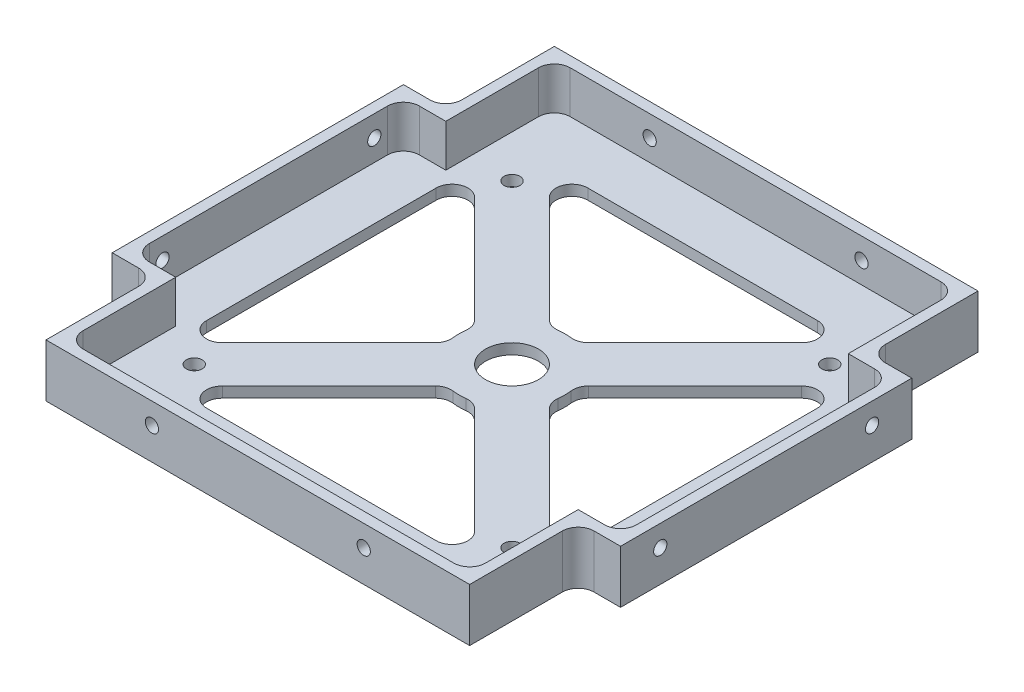
SolidWorks part; units mm, degrees
material "6061-T6 (SS)"
ref_plane "Front Plane" through (0, 0, 0) normal (0, 0, 1) x (1, 0, 0)
ref_plane "Top Plane" through (0, 0, 0) normal (0, 1, 0) x (1, 0, 0)
ref_plane "Right Plane" through (0, 0, 0) normal (1, 0, 0) x (0, 0, -1)
sketch "Sketch1" plane through (0, 0, 0) normal (0, 1, 0) x (1, 0, 0)
  line L0 (0, 8) -> (8, 0)
  line L1 (0, 0) -> (96, 0)
  line L2 (0, 0) -> (0, 96)
  line L3 (0, 96) -> (96, 96)
  line L4 (96, 0) -> (96, 96)
  line L5 (48, 96) -> (48, 0) construction
  line L6 (0, 48) -> (96, 48) construction
  line L7 (96, 8) -> (88, 0)
  line L8 (96, 88) -> (88, 96)
  line L9 (0, 88) -> (8, 96)
  dimension "D1" = 96
  dimension "D2" = 96
  dimension "D3" = 8
  dimension "D4" = 8
extrude "Boss-Extrude1" add sketch "Sketch1" along normal blind 10 contours L9 L2 L0 L1 L7 L4 L8 L3
sketch "Sketch2" plane through (0, 0, 0) normal (0, -1, 0) x (-1, 0, 0)
  line L0 (-4, 92) -> (-92, 4) construction
  line L1 (0, 88) -> (-8, 96) construction
  line L2 (-96, 8) -> (-88, 0) construction
  line L3 (-92, 92) -> (-4, 4) construction
  line L4 (-96, 88) -> (-88, 96) construction
  line L5 (0, 8) -> (-8, 0) construction
  line L6 (-12, 84) -> (-84, 84) construction
  line L7 (-84, 84) -> (-84, 12) construction
  line L8 (-84, 12) -> (-12, 12) construction
  line L9 (-12, 12) -> (-12, 84) construction
  line L10 (-8, 96) -> (-88, 96) construction
  line L12 (-19.0711, 84) -> (-84, 19.0711)
  line L13 (-12, 76.9289) -> (-76.9289, 12)
  line L14 (-12, 19.0711) -> (-76.9289, 84)
  line L15 (-19.0711, 12) -> (-84, 76.9289)
  line L16 (-12, 76.9289) -> (-12, 19.0711)
  line L17 (-19.0711, 12) -> (-76.9289, 12)
  line L18 (-84, 19.0711) -> (-84, 76.9289)
  line L19 (-76.9289, 84) -> (-19.0711, 84)
  circle A0 centre (-48, 48) radius 10
  circle A1 centre (-48, 48) radius 5
  dimension "D6" = 20
  dimension "D7" = 10
  dimension "D1" = 12
  dimension "D2" = 10
  dimension "D3" = 5
  dimension "D4" = 10
  dimension "D5" = 5
extrude "Cut-Extrude1" cut sketch "Sketch2" against normal through all contours A0 L12 L19 L14 | A0 L14 L16 L13 | A0 L13 L17 L15 | A0 L15 L18 L12 | A1
fillet "Fillet1" radius 3 16 edges at (19.0711, 5, -12) (76.9289, 5, -12) (50.5882, 5, -38.3407) (38.3407, 5, -50.5882) (45.4118, 5, -38.3407) (57.6593, 5, -50.5882) (12, 5, -19.0711) (38.3407, 5, -45.4118) (50.5882, 5, -57.6593) (84, 5, -19.0711) (84, 5, -76.9289) (57.6593, 5, -45.4118) (45.4118, 5, -57.6593) (76.9289, 5, -84) (19.0711, 5, -84) (12, 5, -76.9289)
sketch "Sketch5" plane through (0, 10, 0) normal (0, 1, 0) x (1, 0, 0)
  line L0 (8, 0) -> (8, 20.5)
  line L3 (0, 8) -> (8, 0)
  line L4 (0, 8) -> (0, 20.5)
  line L5 (0, 8) -> (0, 88) construction
  line L6 (0, 20.5) -> (8, 20.5)
  line L7 (0, 48) -> (96, 48) construction
  line L8 (96, 8) -> (96, 88) construction
  line L9 (48, 96) -> (48, 0) construction
  line L10 (8, 96) -> (88, 96) construction
  line L11 (8, 0) -> (88, 0) construction
  line L12 (96, 8) -> (88, 0)
  line L13 (96, 8) -> (96, 20.5)
  line L14 (96, 20.5) -> (88, 20.5)
  line L15 (88, 0) -> (88, 20.5)
  line L16 (96, 75.5) -> (88, 75.5)
  line L17 (96, 88) -> (96, 75.5)
  line L18 (96, 88) -> (88, 96)
  line L19 (88, 96) -> (88, 75.5)
  line L20 (8, 96) -> (8, 75.5)
  line L21 (0, 88) -> (8, 96)
  line L22 (0, 88) -> (0, 75.5)
  line L23 (0, 75.5) -> (8, 75.5)
  dimension "D1" = 20.5
extrude "Cut-Extrude4" cut sketch "Sketch5" against normal through all
sketch "Sketch6" plane through (0, 10, 0) normal (0, 1, 0) x (1, 0, 0)
  line L90 (86, 73.5) -> (86, 94)
  line L91 (94, 73.5) -> (86, 73.5)
  line L92 (94, 22.5) -> (94, 73.5)
  line L93 (86, 22.5) -> (94, 22.5)
  line L94 (86, 2) -> (86, 22.5)
  line L95 (10, 2) -> (86, 2)
  line L96 (10, 22.5) -> (10, 2)
  line L97 (2, 22.5) -> (10, 22.5)
  line L98 (2, 73.5) -> (2, 22.5)
  line L99 (10, 73.5) -> (2, 73.5)
  line L100 (10, 94) -> (10, 73.5)
  line L101 (86, 94) -> (10, 94)
  line L102 (86, 73.5) -> (86, 94)
  line L103 (94, 73.5) -> (86, 73.5)
  line L104 (94, 22.5) -> (94, 73.5)
  line L105 (86, 22.5) -> (94, 22.5)
  line L106 (86, 2) -> (86, 22.5)
  line L107 (10, 2) -> (86, 2)
  line L108 (10, 22.5) -> (10, 2)
  line L109 (2, 22.5) -> (10, 22.5)
  line L110 (2, 73.5) -> (2, 22.5)
  line L111 (10, 73.5) -> (2, 73.5)
  line L112 (10, 94) -> (10, 73.5)
  line L113 (86, 94) -> (10, 94)
  dimension "D1" = 2
extrude "Cut-Extrude5" cut sketch "Sketch6" against normal blind 8
fillet "Fillet2" radius 3 12 edges at (88, 5, -75.5) (88, 5, -20.5) (8, 5, -75.5) (8, 5, -20.5) (86, 6, -94) (94, 6, -73.5) (94, 6, -22.5) (86, 6, -2) (10, 6, -94) (10, 6, -2) (2, 6, -22.5) (2, 6, -73.5)
sketch "Sketch7" plane through (0, 0, 0) normal (0, -1, 0) x (1, 0, 0)
  line L0 (78, -18) -> (18, -18) construction
  line L1 (78, -78) -> (18, -78)
  line L2 (78, -78) -> (78, -18)
  line L3 (78, -18) -> (18, -18)
  line L4 (18, -78) -> (18, -18)
  line L5 (78, -78) -> (18, -18) construction
  line L6 (78, -18) -> (18, -78) construction
  line L7 (78, -18) -> (78, -78) construction
  circle A0 centre (78, -18) radius 1.5
  circle A1 centre (18, -18) radius 1.5
  circle A2 centre (18, -78) radius 1.5
  circle A3 centre (78, -78) radius 1.5
  point P0 (48, -48)
  dimension "D1" = 2
  dimension "D2" = 60
  dimension "D3" = 60
extrude "Cut-Extrude6" cut sketch "Sketch7" against normal blind 10 contours A0 | A3 | A2 | A1
sketch "Sketch8" plane through (0, 0, 0) normal (0, 0, 1) x (1, 0, 0)
  line L0 (8, 6) -> (88, 6) construction
  line L1 (8, 10) -> (8, 0) construction
  line L2 (88, 10) -> (88, 0) construction
  line L3 (8, 0) -> (88, 0) construction
  line L4 (48, 10) -> (48, 0) construction
  line L5 (8, 10) -> (88, 10) construction
  line L6 (8, 10) -> (8, 0) construction
  line L7 (88, 0) -> (88, 10) construction
  dimension "D1" = 6
sketch "Sketch9" plane through (0, 0, 0) normal (-1, 0, 0) x (0, 0, 1)
  line L0 (-75.5, 6) -> (-20.5, 6) construction
  line L1 (-75.5, 0) -> (-75.5, 10) construction
  line L2 (-20.5, 0) -> (-20.5, 10) construction
  line L3 (-20.5, 0) -> (-75.5, 0) construction
  line L4 (-48, 10) -> (-48, 0) construction
  line L5 (-20.5, 10) -> (-75.5, 10) construction
  dimension "D1" = 6
hole_wizard "M3x0.5 Tapped Hole1" positions "Sketch12" profile "Sketch13" tap size "M3x0.5" standard "ANSI Metric"
sketch "Sketch12" plane through (0, 0, 0) normal (0, 0, 1) x (1, 0, 0)
  line L0 (8, 6) -> (88, 6) construction
  line L2 (48, 10) -> (48, 0) construction
  point P0 (28, 6)
  point P4 (68, 6)
  dimension "D1" = 40
  dimension "D2" = 20
sketch "Sketch13" plane through (28, 6, 0) normal (1, 0, 0) x (0, -1, 0)
  line L0 (0, 0) -> (0, 8.2511)
  line L1 (0, 8.2511) -> (1.25, 7.5)
  line L2 (1.25, 7.5) -> (1.25, 0)
  line L5 (1.25, 0) -> (0, 0)
  line L10 (0, 8.2511) -> (-1.25, 7.5) construction
  line L11 (0, -6.35) -> (0, 107.95) construction
  dimension "Tap Drill Dia." = 2.5
  dimension "Tap Drill Depth" = 7.5
  dimension "Drill Angle" = 118
hole_wizard "M3x0.5 Tapped Hole2" positions "Sketch14" profile "Sketch15" tap size "M3x0.5" standard "ANSI Metric"
sketch "Sketch14" plane through (0, 0, 0) normal (-1, 0, 0) x (0, 0, 1)
  line L0 (-75.5, 6) -> (-20.5, 6) construction
  line L1 (-48, 10) -> (-48, 0) construction
  point P0 (-68, 6)
  point P4 (-28, 6)
  dimension "D1" = 40
  dimension "D2" = 20
sketch "Sketch15" plane through (0, 6, -68) normal (0, 1, 0) x (0, 0, 1)
  line L0 (0, 0) -> (0, 8.2511)
  line L1 (0, 8.2511) -> (1.25, 7.5)
  line L2 (1.25, 7.5) -> (1.25, 0)
  line L5 (1.25, 0) -> (0, 0)
  line L10 (0, 8.2511) -> (-1.25, 7.5) construction
  line L11 (0, -6.35) -> (0, 107.95) construction
  dimension "Tap Drill Dia." = 2.5
  dimension "Tap Drill Depth" = 7.5
  dimension "Drill Angle" = 118
ref_plane "Plane1" through (48, 0, 0) normal (-1, 0, 0) x (0, 0, 1)
ref_plane "Plane2" through (0, 0, -48) normal (0, 0, 1) x (1, 0, 0)
mirror "Mirror1" about plane through (0, 0, -48) normal (0, 0, 1) of "M3x0.5 Tapped Hole1"
mirror "Mirror2" about plane through (48, 0, 0) normal (-1, 0, 0) of "M3x0.5 Tapped Hole2"
